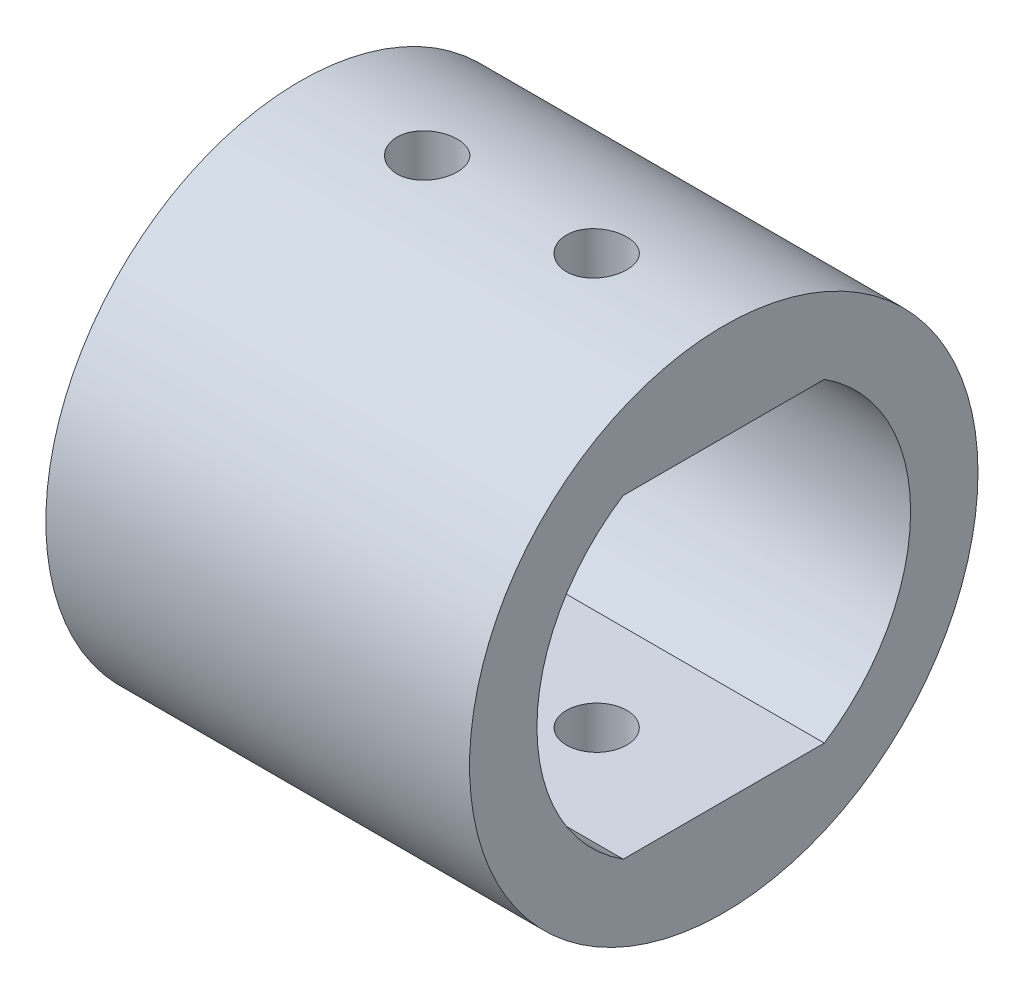
SolidWorks part; units mm, degrees
ref_plane "Front Plane" through (0, 0, 0) normal (0, 0, 1) x (1, 0, 0)
ref_plane "Top Plane" through (0, 0, 0) normal (0, 1, 0) x (1, 0, 0)
ref_plane "Right Plane" through (0, 0, 0) normal (1, 0, 0) x (0, 0, -1)
sketch "Sketch1" plane through (0, 0, 0) normal (1, 0, 0) x (0, 0, -1)
  line L0 (-3.767, 5.9) -> (3.767, 5.9)
  line L1 (-13.9937, 0) -> (13.5802, 0) construction
  line L2 (-3.767, -5.9) -> (3.767, -5.9)
  circle A0 centre (0, 0) radius 7
  circle A1 centre (0, 0) radius 9.525
  dimension "D1" = 14
  dimension "D2" = 19.05
  dimension "D3" = 5.9
extrude "Boss-Extrude1" add sketch "Sketch1" along normal mid plane 15.875 contours A1 L1 A0 | L0 A0 | L1 A1 A0 | L2 A0
ref_plane "Plane1" through (0, 9.525, 0) normal (0, 1, 0) x (1, 0, 0)
sketch "Sketch2" plane through (0, 9.525, 0) normal (0, 1, 0) x (1, 0, 0)
  line L1 (0, 0) -> (3.175, 0) construction
  circle A0 centre (-3.175, 0) radius 1.1303
  circle A1 centre (3.175, 0) radius 1.1303
  point P0 (-3.175, 0)
  point P1 (3.175, 0)
  dimension "D2" = 2.2606
  dimension "D1" = 6.35
extrude "Cut-Extrude1" cut sketch "Sketch2" against normal through all both and the other way through all
